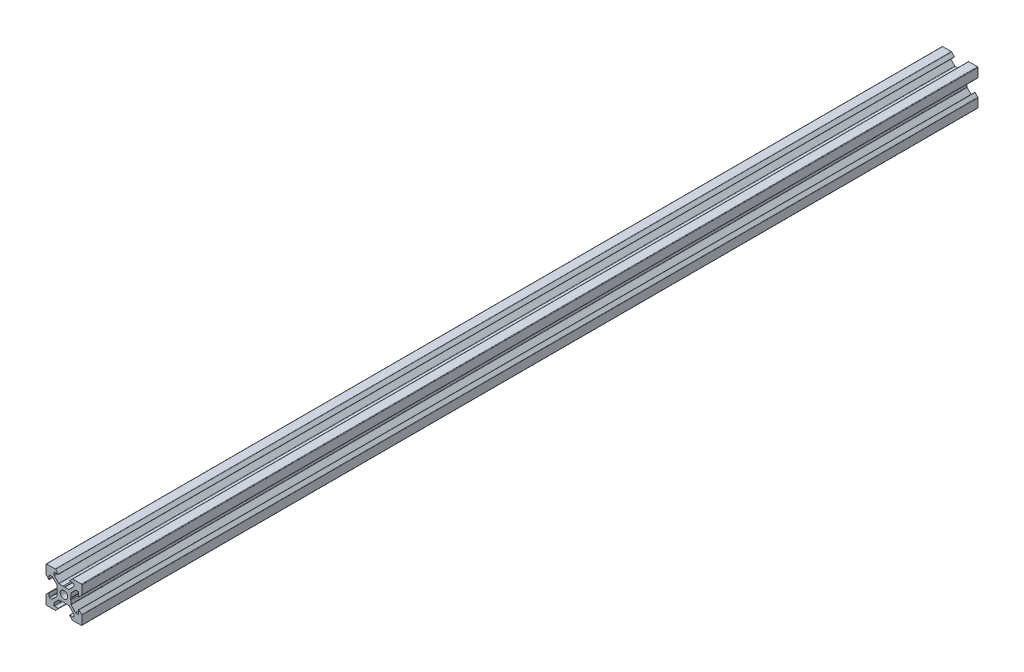
SolidWorks part; units mm, degrees
material "6063-T5"
ref_plane "Plan de face" through (0, 0, 0) normal (0, 0, 1) x (1, 0, 0)
ref_plane "Plan de dessus" through (0, 0, 0) normal (0, 1, 0) x (1, 0, 0)
ref_plane "Plan de droite" through (0, 0, 0) normal (1, 0, 0) x (0, 0, -1)
sketch "Esquisse1" plane through (0, 0, 0) normal (0, 0, 1) x (1, 0, 0)
  line L0 (18.7749, -2.8952) -> (18.7749, -4.8946)
  line L1 (18.4749, -5.1946) -> (17.2591, -5.1946)
  line L2 (17.047, -5.1067) -> (14.5634, -2.6231)
  line L3 (14.4755, -2.411) -> (14.4755, -0.2148)
  line L4 (14.4755, -0.2148) -> (14.1755, 0.3048)
  line L5 (14.1755, 0.3048) -> (14.4755, 0.8244)
  line L6 (14.4755, 0.8244) -> (14.4755, 3.0205)
  line L7 (14.5634, 3.2326) -> (17.047, 5.7162)
  line L8 (17.2591, 5.8041) -> (18.4749, 5.8041)
  line L9 (18.7749, 5.5041) -> (18.7749, 3.5048)
  line L10 (18.9456, 3.4341) -> (20.487, 4.9755)
  line L11 (20.5749, 5.1876) -> (20.5749, 10.0048)
  line L12 (20.2749, 10.3048) -> (15.4577, 10.3048)
  line L13 (15.2456, 10.2169) -> (13.7041, 8.6755)
  line L14 (13.7749, 8.5048) -> (15.7742, 8.5048)
  line L15 (16.0742, 8.2048) -> (16.0742, 6.989)
  line L16 (15.9863, 6.7769) -> (13.5027, 4.2933)
  line L17 (13.2906, 4.2054) -> (11.0945, 4.2054)
  line L18 (11.0945, 4.2054) -> (10.5749, 3.9054)
  line L19 (10.5749, 3.9054) -> (10.0552, 4.2054)
  line L20 (10.0552, 4.2054) -> (7.8591, 4.2054)
  line L21 (7.647, 4.2933) -> (5.1634, 6.7769)
  line L22 (5.0755, 6.989) -> (5.0755, 8.2048)
  line L23 (5.3755, 8.5048) -> (7.3749, 8.5048)
  line L24 (7.4456, 8.6755) -> (5.9041, 10.2169)
  line L25 (5.692, 10.3048) -> (0.8749, 10.3048)
  line L26 (0.5749, 10.0048) -> (0.5749, 5.1876)
  line L27 (0.6627, 4.9755) -> (2.2041, 3.4341)
  line L28 (2.3749, 3.5048) -> (2.3749, 5.5041)
  line L29 (2.6749, 5.8041) -> (3.8906, 5.8041)
  line L30 (4.1027, 5.7162) -> (6.5863, 3.2326)
  line L31 (6.6742, 3.0205) -> (6.6742, 0.8244)
  line L32 (6.6742, 0.8244) -> (6.9742, 0.3048)
  line L33 (6.9742, 0.3048) -> (6.6742, -0.2148)
  line L34 (6.6742, -0.2148) -> (6.6742, -2.411)
  line L35 (6.5863, -2.6231) -> (4.1027, -5.1067)
  line L36 (3.8906, -5.1946) -> (2.6749, -5.1946)
  line L37 (2.3749, -4.8946) -> (2.3749, -2.8952)
  line L38 (2.2041, -2.8245) -> (0.6627, -4.3659)
  line L39 (0.5749, -4.5781) -> (0.5749, -9.3952)
  line L40 (0.8749, -9.6952) -> (5.692, -9.6952)
  line L41 (5.9041, -9.6074) -> (7.4456, -8.0659)
  line L42 (7.3749, -7.8952) -> (5.3755, -7.8952)
  line L43 (5.0755, -7.5952) -> (5.0755, -6.3795)
  line L44 (5.1634, -6.1674) -> (7.647, -3.6838)
  line L45 (7.8591, -3.5959) -> (10.0552, -3.5959)
  line L46 (10.0552, -3.5959) -> (10.5749, -3.2959)
  line L47 (10.5749, -3.2959) -> (11.0945, -3.5959)
  line L48 (11.0945, -3.5959) -> (13.2906, -3.5959)
  line L49 (13.5027, -3.6838) -> (15.9863, -6.1674)
  line L50 (16.0742, -6.3795) -> (16.0742, -7.5952)
  line L51 (15.7742, -7.8952) -> (13.7749, -7.8952)
  line L52 (13.7041, -8.0659) -> (15.2456, -9.6074)
  line L53 (15.4577, -9.6952) -> (20.2749, -9.6952)
  line L54 (20.5749, -9.3952) -> (20.5749, -4.5781)
  line L55 (20.487, -4.3659) -> (18.9456, -2.8245)
  arc A0 (10.5749, -1.7952) -> (12.6749, 0.3048) centre (10.5749, 0.3048) ccw
  arc A1 (12.6749, 0.3048) -> (10.5749, 2.4048) centre (10.5749, 0.3048) ccw
  arc A2 (10.5749, 2.4048) -> (8.4749, 0.3048) centre (10.5749, 0.3048) ccw
  arc A3 (8.4749, 0.3048) -> (10.5749, -1.7952) centre (10.5749, 0.3048) ccw
  arc A4 (18.9456, -2.8245) -> (18.7749, -2.8952) centre (18.8749, -2.8952) ccw
  arc A5 (18.4749, -5.1946) -> (18.7749, -4.8946) centre (18.4749, -4.8946) ccw
  arc A6 (17.047, -5.1067) -> (17.2591, -5.1946) centre (17.2591, -4.8946) ccw
  arc A7 (14.4755, -2.411) -> (14.5634, -2.6231) centre (14.7755, -2.411) ccw
  arc A8 (14.5634, 3.2326) -> (14.4755, 3.0205) centre (14.7755, 3.0205) ccw
  arc A9 (17.2591, 5.8041) -> (17.047, 5.7162) centre (17.2591, 5.5041) ccw
  arc A10 (18.7749, 5.5041) -> (18.4749, 5.8041) centre (18.4749, 5.5041) ccw
  arc A11 (18.7749, 3.5048) -> (18.9456, 3.4341) centre (18.8749, 3.5048) ccw
  arc A12 (20.487, 4.9755) -> (20.5749, 5.1876) centre (20.2749, 5.1876) ccw
  arc A13 (20.5749, 10.0048) -> (20.2749, 10.3048) centre (20.2749, 10.0048) ccw
  arc A14 (15.4577, 10.3048) -> (15.2456, 10.2169) centre (15.4577, 10.0048) ccw
  arc A15 (13.7041, 8.6755) -> (13.7749, 8.5048) centre (13.7749, 8.6048) ccw
  arc A16 (16.0742, 8.2048) -> (15.7742, 8.5048) centre (15.7742, 8.2048) ccw
  arc A17 (15.9863, 6.7769) -> (16.0742, 6.989) centre (15.7742, 6.989) ccw
  arc A18 (13.2906, 4.2054) -> (13.5027, 4.2933) centre (13.2906, 4.5054) ccw
  arc A19 (7.647, 4.2933) -> (7.8591, 4.2054) centre (7.8591, 4.5054) ccw
  arc A20 (5.0755, 6.989) -> (5.1634, 6.7769) centre (5.3755, 6.989) ccw
  arc A21 (5.3755, 8.5048) -> (5.0755, 8.2048) centre (5.3755, 8.2048) ccw
  arc A22 (7.3749, 8.5048) -> (7.4456, 8.6755) centre (7.3749, 8.6048) ccw
  arc A23 (5.9041, 10.2169) -> (5.692, 10.3048) centre (5.692, 10.0048) ccw
  arc A24 (0.8749, 10.3048) -> (0.5749, 10.0048) centre (0.8749, 10.0048) ccw
  arc A25 (0.5749, 5.1876) -> (0.6627, 4.9755) centre (0.8749, 5.1876) ccw
  arc A26 (2.2041, 3.4341) -> (2.3749, 3.5048) centre (2.2749, 3.5048) ccw
  arc A27 (2.6749, 5.8041) -> (2.3749, 5.5041) centre (2.6749, 5.5041) ccw
  arc A28 (4.1027, 5.7162) -> (3.8906, 5.8041) centre (3.8906, 5.5041) ccw
  arc A29 (6.6742, 3.0205) -> (6.5863, 3.2326) centre (6.3742, 3.0205) ccw
  arc A30 (6.5863, -2.6231) -> (6.6742, -2.411) centre (6.3742, -2.411) ccw
  arc A31 (3.8906, -5.1946) -> (4.1027, -5.1067) centre (3.8906, -4.8946) ccw
  arc A32 (2.3749, -4.8946) -> (2.6749, -5.1946) centre (2.6749, -4.8946) ccw
  arc A33 (2.3749, -2.8952) -> (2.2041, -2.8245) centre (2.2749, -2.8952) ccw
  arc A34 (0.6627, -4.3659) -> (0.5749, -4.5781) centre (0.8749, -4.5781) ccw
  arc A35 (0.5749, -9.3952) -> (0.8749, -9.6952) centre (0.8749, -9.3952) ccw
  arc A36 (5.692, -9.6952) -> (5.9041, -9.6074) centre (5.692, -9.3952) ccw
  arc A37 (7.4456, -8.0659) -> (7.3749, -7.8952) centre (7.3749, -7.9952) ccw
  arc A38 (5.0755, -7.5952) -> (5.3755, -7.8952) centre (5.3755, -7.5952) ccw
  arc A39 (5.1634, -6.1674) -> (5.0755, -6.3795) centre (5.3755, -6.3795) ccw
  arc A40 (7.8591, -3.5959) -> (7.647, -3.6838) centre (7.8591, -3.8959) ccw
  arc A41 (13.5027, -3.6838) -> (13.2906, -3.5959) centre (13.2906, -3.8959) ccw
  arc A42 (16.0742, -6.3795) -> (15.9863, -6.1674) centre (15.7742, -6.3795) ccw
  arc A43 (15.7742, -7.8952) -> (16.0742, -7.5952) centre (15.7742, -7.5952) ccw
  arc A44 (13.7749, -7.8952) -> (13.7041, -8.0659) centre (13.7749, -7.9952) ccw
  arc A45 (15.2456, -9.6074) -> (15.4577, -9.6952) centre (15.4577, -9.3952) ccw
  arc A46 (20.2749, -9.6952) -> (20.5749, -9.3952) centre (20.2749, -9.3952) ccw
  arc A47 (20.5749, -4.5781) -> (20.487, -4.3659) centre (20.2749, -4.5781) ccw
extrude "Boss.-Extru.1" add sketch "Esquisse1" along normal blind 500
